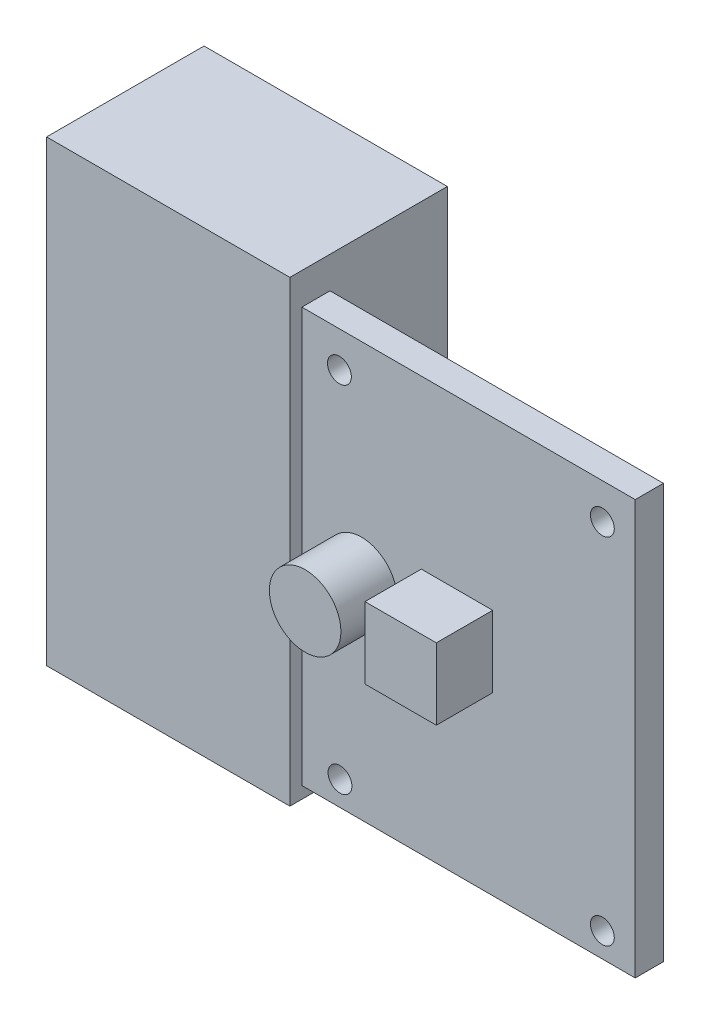
SolidWorks part; units mm, degrees
ref_plane "Front Plane" through (0, 0, 0) normal (0, 0, 1) x (1, 0, 0)
ref_plane "Top Plane" through (0, 0, 0) normal (0, 1, 0) x (1, 0, 0)
ref_plane "Right Plane" through (0, 0, 0) normal (1, 0, 0) x (0, 0, -1)
sketch "Sketch1" plane through (0, 0, 0) normal (0, 0, 1) x (1, 0, 0)
  line L1 (0, 0) -> (-35.5, 0)
  line L2 (0, 0) -> (0, 44.12)
  line L3 (0, 44.12) -> (-35.5, 44.12)
  line L4 (-35.5, 0) -> (-35.5, 44.12)
  line L5 (-22.78, 26.32) -> (-15.18, 26.32)
  line L6 (-22.78, 26.32) -> (-22.78, 18.72)
  line L7 (-22.78, 18.72) -> (-15.18, 18.72)
  line L8 (-15.18, 26.32) -> (-15.18, 18.72)
  circle A0 centre (-29.15, 22.276) radius 3.81
  circle A1 centre (-31.44, 2.6) radius 1.27
  circle A2 centre (-3.5, 2.6) radius 1.27
  circle A3 centre (-3.5, 40.32) radius 1.27
  circle A4 centre (-31.5, 40.32) radius 1.27
  point P19 (0, 0)
  point P20 (0, 0)
  point P21 (0, 0)
  point P22 (0, 0)
  point P23 (0, 0)
  point P24 (0, 0)
  point P25 (0, 0)
  point P26 (-1.4721, 2.7579)
  point P27 (0, 0)
  point P28 (0, 0)
  point P29 (0, 0)
  point P30 (0, 0)
  point P31 (0, 0)
  point P32 (0, 0)
  point P33 (0, 0)
  point P34 (0, 0)
  point P35 (0, 0)
  point P36 (0, 0)
  dimension "D4" = 7.62
  dimension "D10" = 2.54
  dimension "D11" = 2.54
  dimension "D12" = 2.54
  dimension "D13" = 2.54
  dimension "D14" = 4
  dimension "D1" = 35.5
  dimension "D2" = 44.12
  dimension "D3" = 6.35
  dimension "D5" = 13.97
  dimension "D6" = 2.6
  dimension "D7" = 7.6
  dimension "D8" = 7.6
  dimension "D9" = 25.4
  dimension "D15" = 0
  dimension "D16" = 3.8
  dimension "D17" = 28
  dimension "D18" = 27.94
  dimension "D19" = 0
  dimension "D20" = 0
  dimension "D21" = 35.5
  dimension "D22" = 21.844
extrude "Boss-Extrude1" add sketch "Sketch1" along normal blind 3
sketch "Sketch2" plane through (0, 0, 3) normal (0, 0, 1) x (1, 0, 0)
  line L0 (-35.5, 44.12) -> (-35.5, 0) construction
  line L1 (-62.678, 46.228) -> (-36.77, 46.228)
  line L2 (-62.678, 46.228) -> (-62.678, -2.54)
  line L3 (-62.678, -2.54) -> (-36.77, -2.54)
  line L4 (-36.77, 46.228) -> (-36.77, -2.54)
  line L5 (-35.5, 0) -> (0, 0) construction
  dimension "D1" = 48.768
  dimension "D2" = 25.908
  dimension "D3" = 1.27
  dimension "D4" = 2.54
extrude "Boss-Extrude4" add sketch "Sketch2" along normal blind 0.0025 and the other way blind 16.764 separate body
sketch "Sketch3" plane through (0, 0, 3) normal (0, 0, 1) x (1, 0, 0)
  line L1 (-15.18, 18.72) -> (-22.78, 18.72)
  line L2 (-15.18, 18.72) -> (-15.18, 26.32)
  line L3 (-15.18, 26.32) -> (-22.78, 26.32)
  line L4 (-22.78, 18.72) -> (-22.78, 26.32)
  circle A0 centre (-29.15, 22.276) radius 3.81
  point P10 (0, 0)
extrude "Boss-Extrude5" add sketch "Sketch3" along normal blind 6 separate body
